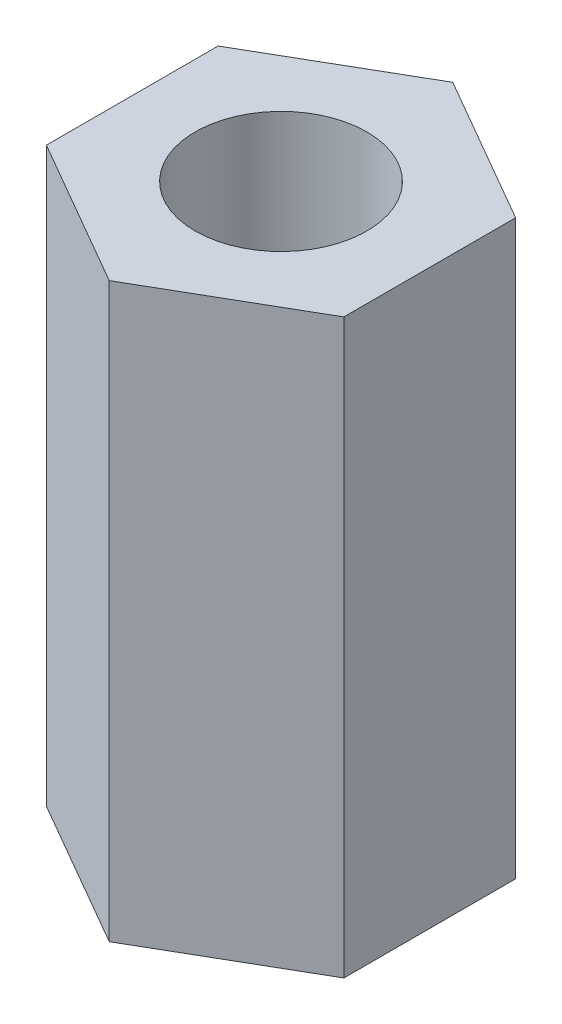
SolidWorks part; units mm, degrees
ref_plane "Face" through (0, 0, 0) normal (0, 0, 1) x (1, 0, 0)
ref_plane "Dessus" through (0, 0, 0) normal (0, 1, 0) x (1, 0, 0)
ref_plane "Droite" through (0, 0, 0) normal (1, 0, 0) x (0, 0, -1)
sketch "Esquisse1" plane through (0, 0, 0) normal (0, 1, 0) x (1, 0, 0)
  line L0 (0, 0) -> (0, 5.5688) construction
  line L1 (0, 3) -> (-2.5981, 1.5)
  line L2 (-2.5981, 1.5) -> (-2.5981, -1.5)
  line L3 (-2.5981, -1.5) -> (0, -3)
  line L4 (0, -3) -> (2.5981, -1.5)
  line L5 (2.5981, -1.5) -> (2.5981, 1.5)
  line L6 (2.5981, 1.5) -> (0, 3)
  circle A0 centre (0, 0) radius 2.5981 construction
  circle A1 centre (0, 0) radius 1.5
  dimension "D1" = 6
  dimension "D2" = 3
extrude "Extrusion1" add sketch "Esquisse1" along normal blind 10
